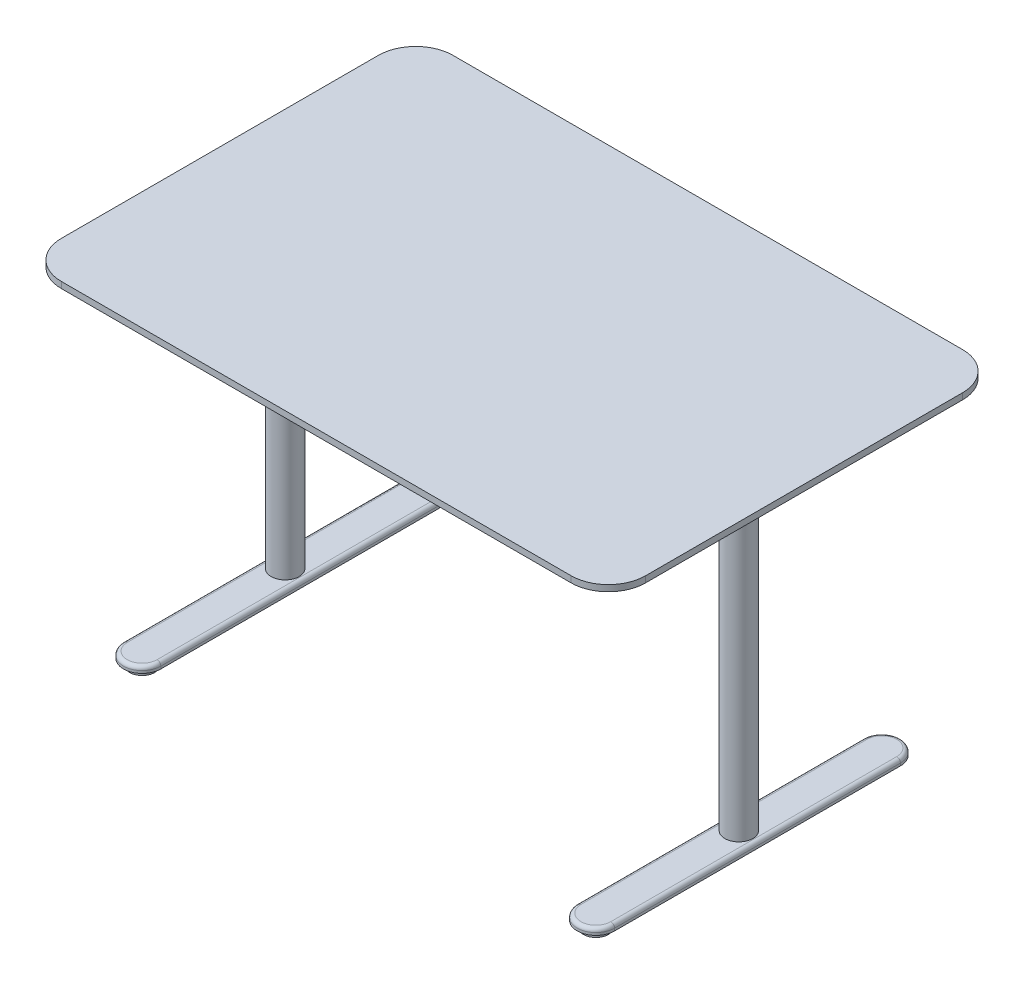
SolidWorks part; units mm, degrees
ref_plane "Front Plane" through (0, 0, 0) normal (0, 0, 1) x (1, 0, 0)
ref_plane "Top Plane" through (0, 0, 0) normal (0, 1, 0) x (1, 0, 0)
ref_plane "Right Plane" through (0, 0, 0) normal (1, 0, 0) x (0, 0, -1)
sketch "Sketch1" plane through (0, 0, 0) normal (0, 1, 0) x (1, 0, 0)
  line L1 (-520.7, 400.05) -> (520.7, 400.05)
  line L2 (-596.9, 323.85) -> (-596.9, -323.85)
  line L3 (-520.7, -400.05) -> (520.7, -400.05)
  line L4 (596.9, 323.85) -> (596.9, -323.85)
  line L5 (-596.9, 400.05) -> (596.9, -400.05) construction
  line L6 (-596.9, -400.05) -> (596.9, 400.05) construction
  arc A0 (520.7, 400.05) -> (596.9, 323.85) centre (520.7, 323.85) cw
  arc A1 (520.7, -400.05) -> (596.9, -323.85) centre (520.7, -323.85) ccw
  arc A2 (-596.9, -323.85) -> (-520.7, -400.05) centre (-520.7, -323.85) ccw
  arc A3 (-520.7, 400.05) -> (-596.9, 323.85) centre (-520.7, 323.85) ccw
  point P0 (0, 0)
  dimension "D3" = 76.2
  dimension "D1" = 1193.8
  dimension "D2" = 800.1
extrude "Boss-Extrude1" add sketch "Sketch1" against normal blind 12.7
sketch "Sketch2" plane through (0, -12.7, 0) normal (0, -1, 0) x (1, 0, 0)
  line L1 (-527.05, 228.6) -> (527.05, 228.6)
  line L2 (-527.05, 228.6) -> (-527.05, -228.6)
  line L3 (-527.05, -228.6) -> (527.05, -228.6)
  line L4 (527.05, 228.6) -> (527.05, -228.6)
  line L5 (-527.05, 228.6) -> (527.05, -228.6) construction
  line L6 (-527.05, -228.6) -> (527.05, 228.6) construction
  point P0 (0, 0)
  dimension "D1" = 1054.1
  dimension "D2" = 457.2
extrude "Extrude-Thin1" add sketch "Sketch2" along normal blind 31.75 thin
sketch "Sketch3" plane through (0, -12.7, 0) normal (0, -1, 0) x (1, 0, 0)
  line L0 (495.3, 196.85) -> (-495.3, 196.85) construction
  line L1 (-431.8, 196.85) -> (-400.05, 196.85)
  line L2 (-431.8, 196.85) -> (-431.8, -196.85)
  line L3 (-431.8, -196.85) -> (-400.05, -196.85)
  line L4 (-400.05, 196.85) -> (-400.05, -196.85)
  line L5 (-495.3, -196.85) -> (495.3, -196.85) construction
  line L6 (-495.3, 196.85) -> (-495.3, -196.85) construction
  line L7 (0, 0) -> (0, 478.9477) construction
  line L8 (400.05, 196.85) -> (400.05, -196.85)
  line L9 (431.8, -196.85) -> (400.05, -196.85)
  line L10 (431.8, 196.85) -> (431.8, -196.85)
  line L11 (431.8, 196.85) -> (400.05, 196.85)
  dimension "D1" = 63.5
  dimension "D2" = 31.75
extrude "Boss-Extrude2" add sketch "Sketch3" along normal up to surface (31.75 mm away) separate body up to face at (0, -44.45, 0)
sketch "Sketch4" plane through (0, -44.45, 0) normal (0, -1, 0) x (1, 0, 0)
  line L0 (-495.3, 196.85) -> (-495.3, -196.85) construction
  line L1 (-495.3, -44.45) -> (-431.8, -44.45)
  line L2 (-495.3, -44.45) -> (-495.3, 44.45)
  line L3 (-495.3, 44.45) -> (-431.8, 44.45)
  line L4 (-431.8, -44.45) -> (-431.8, 44.45)
  line L5 (-431.8, 196.85) -> (-431.8, -196.85) construction
  line L6 (0, 0) -> (0, 493.0588) construction
  line L7 (0, 0) -> (-431.8, 0) construction
  line L8 (431.8, -44.45) -> (431.8, 44.45)
  line L9 (495.3, 44.45) -> (431.8, 44.45)
  line L10 (495.3, -44.45) -> (495.3, 44.45)
  line L11 (495.3, -44.45) -> (431.8, -44.45)
  dimension "D1" = 88.9
extrude "Boss-Extrude3" add sketch "Sketch4" against normal blind 12.7 separate body
sketch "Sketch5" plane through (0, -44.45, 0) normal (0, -1, 0) x (1, 0, 0)
  line L0 (0, 0) -> (-463.55, 0) construction
  line L1 (0, 0) -> (0, 515.4706) construction
  line L3 (-431.8, 44.45) -> (-495.3, 44.45) construction
  line L4 (-463.55, 44.45) -> (-463.55, 0) construction
  circle A0 centre (-463.55, 0) radius 28.575
  circle A1 centre (463.55, 0) radius 28.575
  dimension "D1" = 57.15
extrude "Boss-Extrude4" add sketch "Sketch5" along normal blind 635 separate body
sketch "Sketch6" plane through (0, -679.45, 0) normal (0, -1, 0) x (1, 0, 0)
  line L0 (-463.55, -292.1) -> (-463.55, 292.1) construction
  line L1 (-501.65, -292.1) -> (-501.65, 292.1)
  line L2 (-425.45, -292.1) -> (-425.45, 292.1)
  line L3 (0, 0) -> (0, 564.3775) construction
  line L4 (463.55, -292.1) -> (463.55, 292.1) construction
  line L5 (501.65, -292.1) -> (501.65, 292.1)
  line L6 (425.45, -292.1) -> (425.45, 292.1)
  arc A0 (-501.65, -292.1) -> (-425.45, -292.1) centre (-463.55, -292.1) ccw
  arc A1 (-425.45, 292.1) -> (-501.65, 292.1) centre (-463.55, 292.1) ccw
  arc A2 (501.65, -292.1) -> (425.45, -292.1) centre (463.55, -292.1) cw
  arc A3 (425.45, 292.1) -> (501.65, 292.1) centre (463.55, 292.1) cw
  point P2 (-463.55, 0)
  point P13 (463.55, 0)
  dimension "D1" = 76.2
  dimension "D2" = 660.4
extrude "Boss-Extrude5" add sketch "Sketch6" along normal blind 12.7 separate body
sketch "Sketch7" plane through (0, -692.15, 0) normal (0, -1, 0) x (1, 0, 0)
  circle A0 centre (-463.55, 292.1) radius 25.4
  circle A1 centre (-463.55, -292.1) radius 25.4
  circle A2 centre (463.55, -292.1) radius 25.4
  circle A3 centre (463.55, 292.1) radius 25.4
  dimension "D1" = 50.8
extrude "Boss-Extrude6" add sketch "Sketch7" along normal blind 12.7
fillet "Fillet1" radius 7.62 4 edges at (-463.55, -679.45, 330.2) (-425.45, -679.45, 0) (-463.55, -679.45, -330.2) (-501.65, -679.45, 0)
fillet "Fillet2" radius 7.62 4 edges at (463.55, -679.45, -330.2) (425.45, -679.45, 0) (463.55, -679.45, 330.2) (501.65, -679.45, 0)
